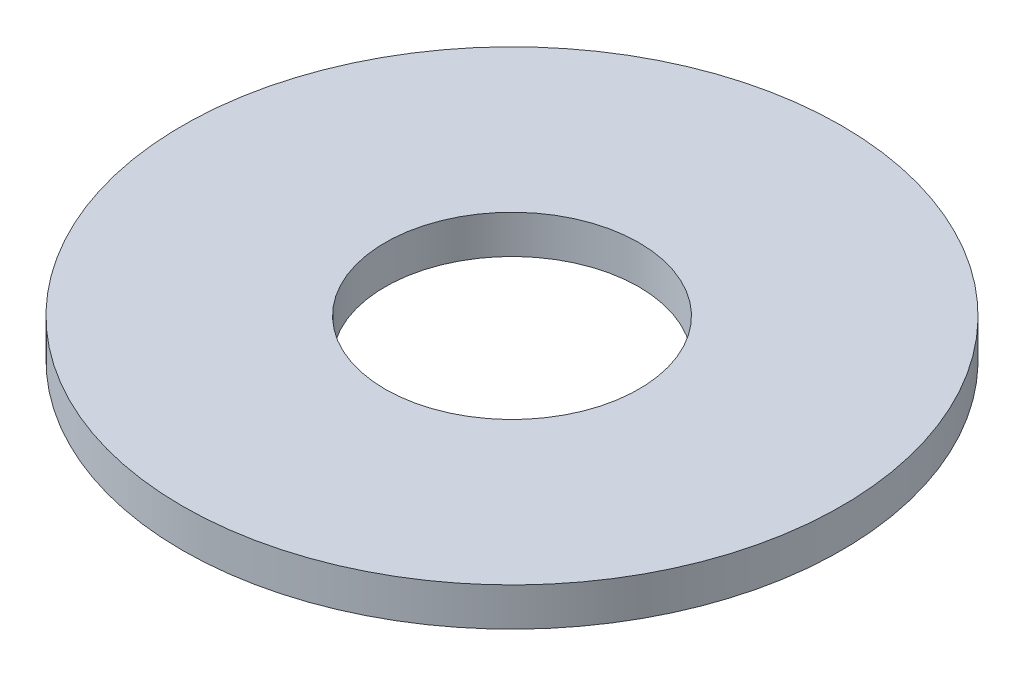
SolidWorks part; units mm, degrees
ref_plane "Front Plane" through (0, 0, 0) normal (0, 0, 1) x (1, 0, 0)
ref_plane "Top Plane" through (0, 0, 0) normal (0, 1, 0) x (1, 0, 0)
ref_plane "Right Plane" through (0, 0, 0) normal (1, 0, 0) x (0, 0, -1)
sketch "Sketch1" plane through (0, 0, 0) normal (0, 1, 0) x (1, 0, 0)
  circle A0 centre (0, 0) radius 3.3655
  circle A1 centre (0, 0) radius 8.7376
  dimension "D1" = 6.731
  dimension "D2" = 17.4752
extrude "Boss-Extrude1" add sketch "Sketch1" along normal blind 1.016
